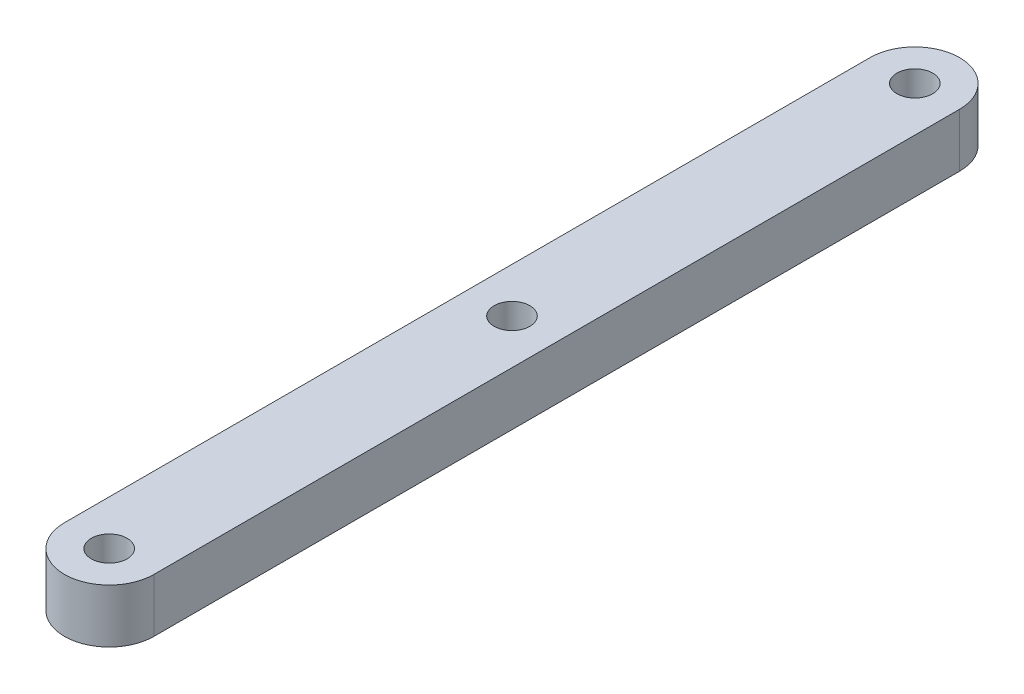
SolidWorks part; units mm, degrees
ref_plane "Front Plane" through (0, 0, 0) normal (0, 0, 1) x (1, 0, 0)
ref_plane "Top Plane" through (0, 0, 0) normal (0, 1, 0) x (1, 0, 0)
ref_plane "Right Plane" through (0, 0, 0) normal (1, 0, 0) x (0, 0, -1)
sketch "Sketch1" plane through (0, 0, 0) normal (0, 1, 0) x (1, 0, 0)
  line L0 (0, 22.5) -> (0, -22.5) construction
  line L1 (2.5, 22.5) -> (2.5, -22.5)
  line L2 (-2.5, 22.5) -> (-2.5, -22.5)
  arc A0 (2.5, 22.5) -> (-2.5, 22.5) centre (0, 22.5) ccw
  arc A1 (-2.5, -22.5) -> (2.5, -22.5) centre (0, -22.5) ccw
  circle A2 centre (0, 22.5) radius 1
  circle A3 centre (0, -22.5) radius 1
  circle A4 centre (0, 0) radius 1
  point P2 (0, 0)
  dimension "D3" = 2
  dimension "D1" = 45
  dimension "D2" = 5
extrude "Boss-Extrude1" add sketch "Sketch1" along normal blind 3
